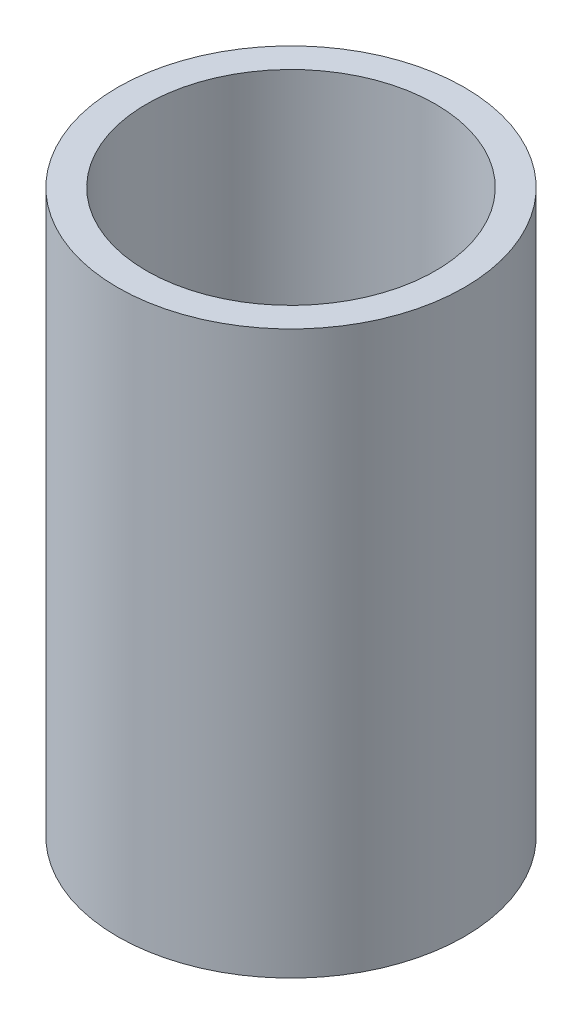
SolidWorks part; units mm, degrees
ref_plane "Front Plane" through (0, 0, 0) normal (0, 0, 1) x (1, 0, 0)
ref_plane "Top Plane" through (0, 0, 0) normal (0, 1, 0) x (1, 0, 0)
ref_plane "Right Plane" through (0, 0, 0) normal (1, 0, 0) x (0, 0, -1)
sketch "Sketch1" plane through (0, 0, 0) normal (0, 1, 0) x (1, 0, 0)
  circle A0 centre (0, 0) radius 2.3813
  circle A1 centre (0, 0) radius 1.9844
  dimension "D1" = 3.9688
  dimension "D2" = 4.7625
extrude "Extrude1" add sketch "Sketch1" along normal blind 7.7216
split "Split1"
